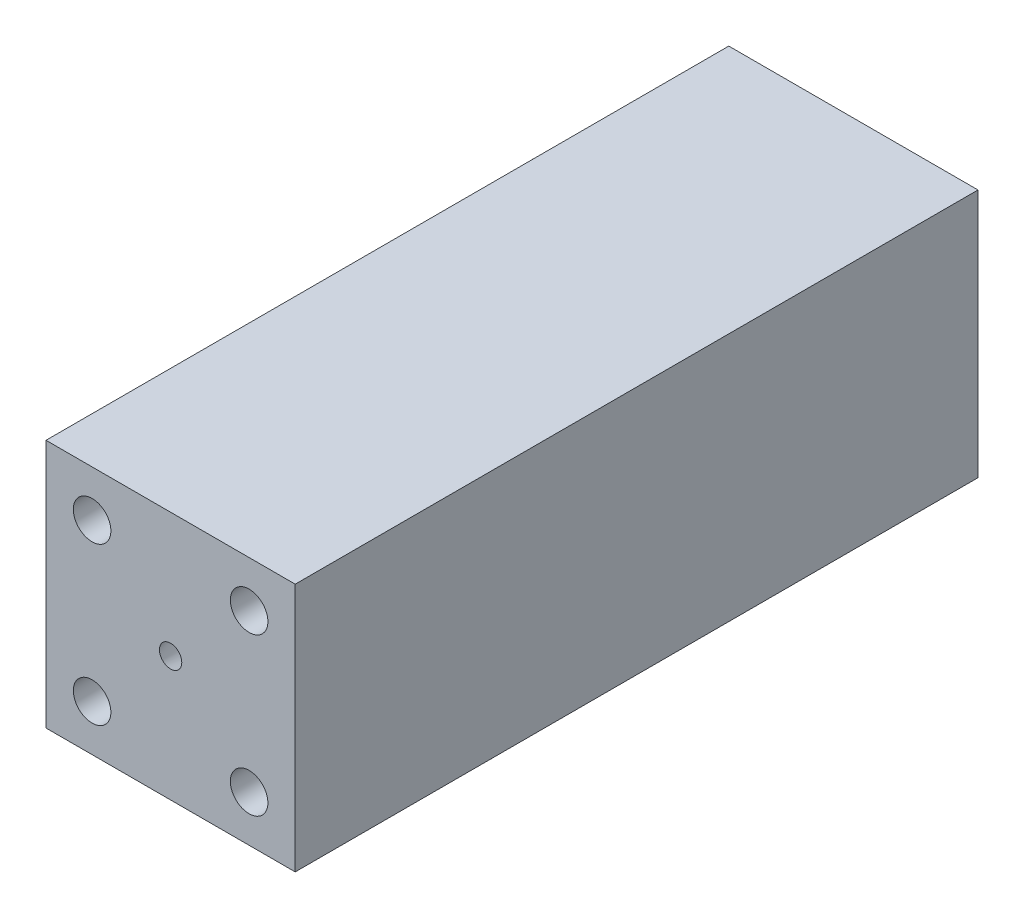
SolidWorks part; units mm, degrees
ref_plane "Front Plane" through (0, 0, 0) normal (0, 0, 1) x (1, 0, 0)
ref_plane "Top Plane" through (0, 0, 0) normal (0, 1, 0) x (1, 0, 0)
ref_plane "Right Plane" through (0, 0, 0) normal (1, 0, 0) x (0, 0, -1)
sketch "Sketch1" plane through (0, 0, 0) normal (0, 0, 1) x (1, 0, 0)
  line L1 (-23.1775, 23.1775) -> (23.1775, 23.1775)
  line L2 (-23.1775, 23.1775) -> (-23.1775, -23.1775)
  line L3 (-23.1775, -23.1775) -> (23.1775, -23.1775)
  line L4 (23.1775, 23.1775) -> (23.1775, -23.1775)
  dimension "D1" = 46.355
  dimension "D2" = 46.355
  dimension "D3" = 23.1775
  dimension "D4" = 23.1775
extrude "Boss-Extrude1" add sketch "Sketch1" along normal blind 127
sketch "Sketch2" plane through (0, 0, 127) normal (0, 0, 1) x (1, 0, 0)
  circle A0 centre (0, 0) radius 1.397
  dimension "D1" = 2.794
extrude "Cut-Extrude1" cut sketch "Sketch2" against normal through all
sketch "Sketch3" plane through (0, 0, 127) normal (0, 0, 1) x (1, 0, 0)
  line L1 (-12.7, 12.7) -> (12.7, 12.7)
  line L2 (-12.7, 12.7) -> (-12.7, -12.7)
  line L3 (-12.7, -12.7) -> (12.7, -12.7)
  line L4 (12.7, 12.7) -> (12.7, -12.7)
  dimension "D1" = 25.4
  dimension "D2" = 25.4
  dimension "D3" = 12.7
  dimension "D4" = 12.7
extrude "Cut-Extrude2" [suppressed] cut sketch "Sketch3" against normal blind 76.2
sketch "Sketch4" plane through (0, 0, 127) normal (0, 0, 1) x (1, 0, 0)
  line L0 (0, 0) -> (30.5635, 0) construction
  line L1 (0, 0) -> (25.1205, 25.1205) construction
  circle A0 centre (14.6019, 14.6019) radius 3.4925
  dimension "D3" = 6.985
  dimension "D1" = 20.6502
  dimension "D2" = 45
extrude "Cut-Extrude3" cut sketch "Sketch4" against normal through all
mirror "Mirror1" about plane through (0, 0, 0) normal (0, 1, 0) of "Cut-Extrude3"
mirror "Mirror2" about plane through (0, 0, 0) normal (1, 0, 0) of "Mirror1", "Cut-Extrude3"
sketch "Sketch5" plane through (0, 0, 0) normal (1, 0, 0) x (0, 0, -1)
  line L0 (0, 14.6019) -> (-44.7122, 14.6019)
  line L1 (0, 14.6019) -> (-127, 14.6019) construction
  line L2 (0, 23.1775) -> (0, -23.1775) construction
  line L3 (-44.7122, 14.6019) -> (-70.5849, 2.0783)
  line L4 (-70.5849, 2.0783) -> (-70.5849, 13.3434)
  line L5 (-70.5849, 13.3434) -> (-87.297, 13.3434)
  line L6 (-87.297, 13.3434) -> (-127, 2.0783)
  line L7 (-127, 23.1775) -> (-127, -23.1775) construction
  line L8 (-127, 2.0783) -> (-127, 0)
  line L9 (-127, 0) -> (0, 0)
  line L10 (0, 0) -> (0, 14.6019)
revolve "Cut-Revolve1" cut sketch "Sketch5" angle 360 about L9
equation "\"D4@Sketch1\"=\"D1@Sketch1\"/2"
equation "\"D3@Sketch1\"=\"D2@Sketch1\"/2"
equation "\"D2@Sketch3\"=\"D1@Sketch3\""
equation "\"D3@Sketch3\"=\"D2@Sketch3\"/2"
equation "\"D4@Sketch3\"=\"D1@Sketch3\"/2"
equation "\"D2@Sketch1\"=\"D1@Sketch1\""
